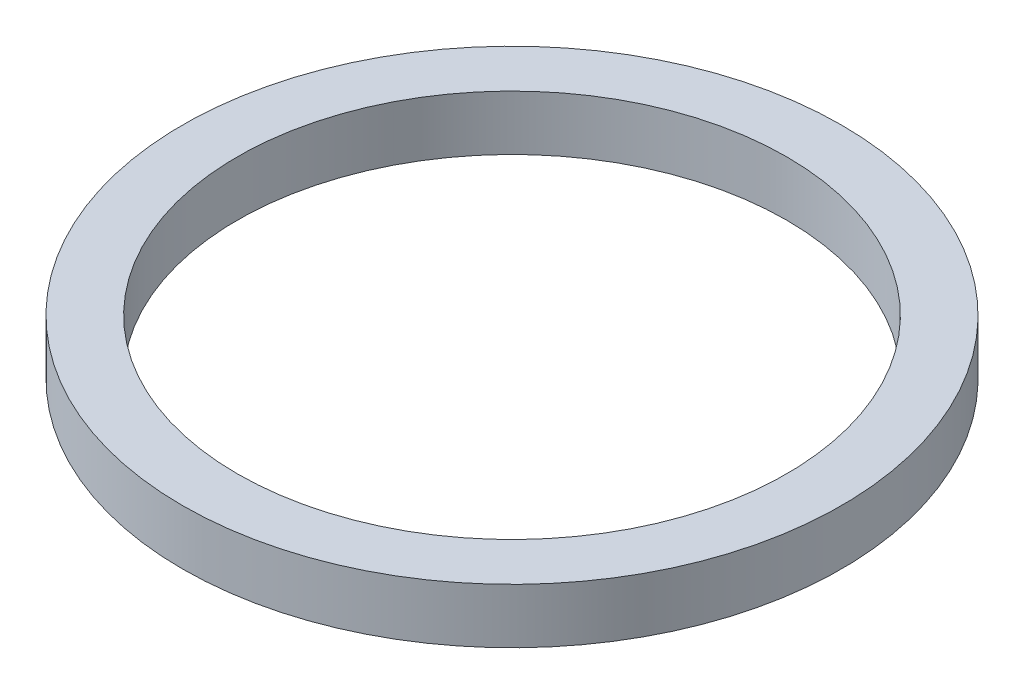
SolidWorks part; units mm, degrees
ref_plane "Front Plane" through (0, 0, 0) normal (0, 0, 1) x (1, 0, 0)
ref_plane "Top Plane" through (0, 0, 0) normal (0, 1, 0) x (1, 0, 0)
ref_plane "Right Plane" through (0, 0, 0) normal (1, 0, 0) x (0, 0, -1)
sketch "Sketch1" plane through (0, 0, 0) normal (0, 1, 0) x (1, 0, 0)
  circle A0 centre (0, 0) radius 2.5
  circle A1 centre (0, 0) radius 3
  dimension "D1" = 5
extrude "Boss-Extrude1" add sketch "Sketch1" along normal blind 0.5
